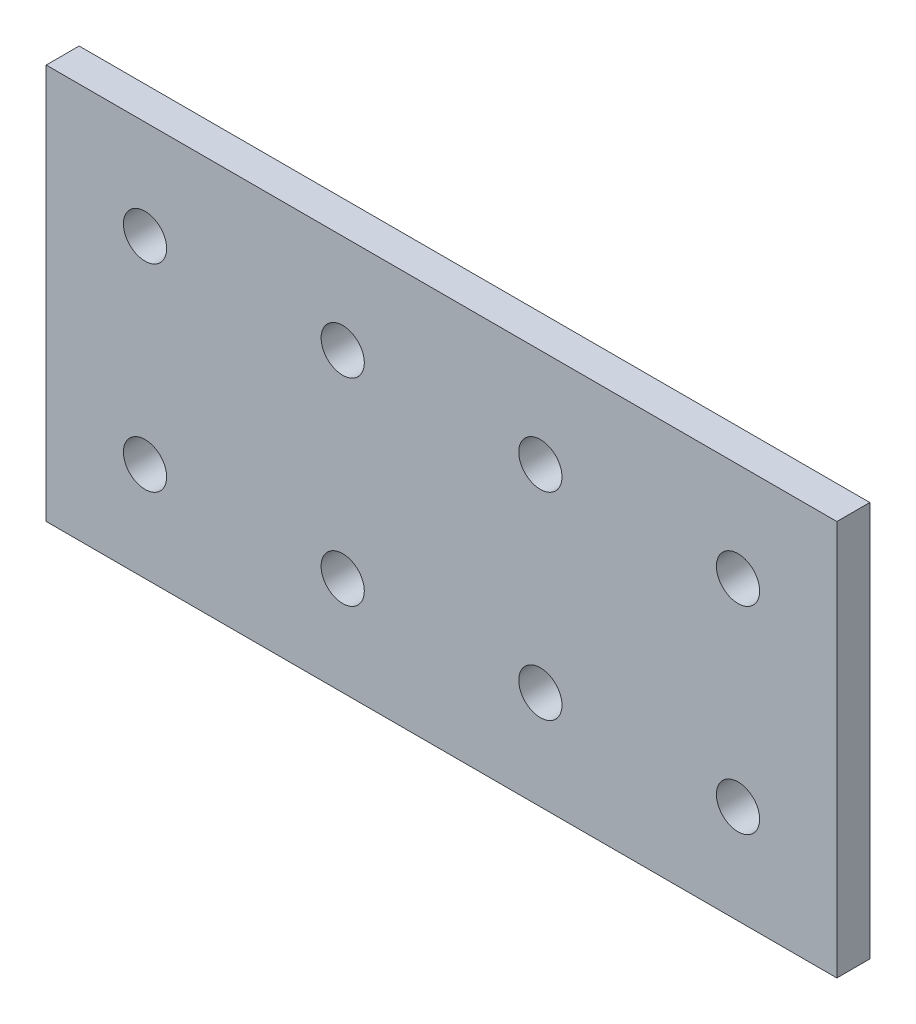
SolidWorks part; units mm, degrees
ref_plane "Front Plane" through (0, 0, 0) normal (0, 0, 1) x (1, 0, 0)
ref_plane "Top Plane" through (0, 0, 0) normal (0, 1, 0) x (1, 0, 0)
ref_plane "Right Plane" through (0, 0, 0) normal (1, 0, 0) x (0, 0, -1)
sketch "Sketch1" plane through (0, 0, 0) normal (0, 0, 1) x (1, 0, 0)
  line L0 (0, 0) -> (0, 76.2)
  line L1 (19.05, 19.05) -> (57.15, 19.05) construction
  line L2 (57.15, 19.05) -> (95.25, 19.05) construction
  line L3 (95.25, 19.05) -> (133.35, 19.05) construction
  line L4 (152.4, 76.2) -> (0, 76.2)
  line L5 (152.4, 0) -> (0, 0)
  line L6 (19.05, 19.05) -> (19.05, 57.15) construction
  line L7 (152.4, 76.2) -> (152.4, 0)
  line L8 (19.05, 57.15) -> (57.15, 57.15) construction
  line L9 (57.15, 57.15) -> (95.25, 57.15) construction
  line L10 (95.25, 57.15) -> (133.35, 57.15) construction
  line L11 (57.15, 19.05) -> (57.15, 57.15) construction
  line L12 (95.25, 19.05) -> (95.25, 57.15) construction
  line L13 (133.35, 19.05) -> (133.35, 57.15) construction
  circle A0 centre (19.05, 19.05) radius 4.1656
  circle A1 centre (57.15, 19.05) radius 4.1656
  circle A2 centre (95.25, 19.05) radius 4.1656
  circle A3 centre (133.35, 19.05) radius 4.1656
  circle A4 centre (19.05, 57.15) radius 4.1656
  circle A5 centre (57.15, 57.15) radius 4.1656
  circle A6 centre (95.25, 57.15) radius 4.1656
  circle A7 centre (133.35, 57.15) radius 4.1656
  dimension "D1" = 38.1
  dimension "E" = 8.3312
  dimension "D2" = 19.05
  dimension "C" = 76.2
  dimension "D3" = 19.05
  dimension "B" = 152.4
extrude "Boss-Extrude1" add sketch "Sketch1" along normal mid plane 6.35
